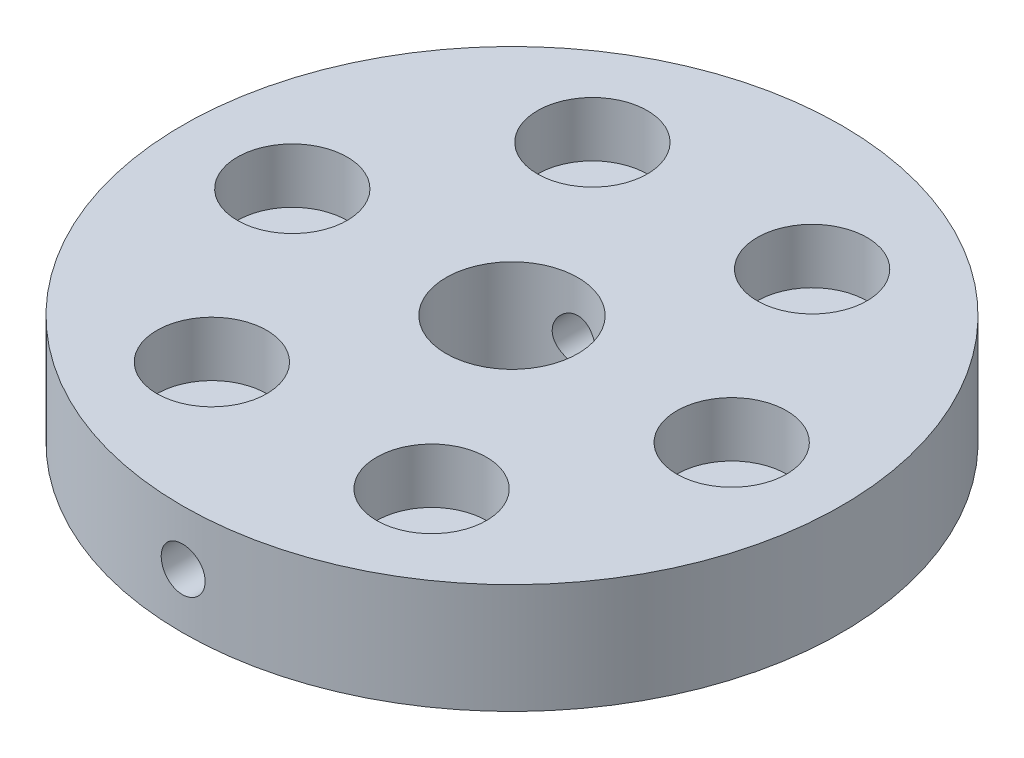
SolidWorks part; units mm, degrees
material "ABS"
ref_plane "Front Plane" through (0, 0, 0) normal (0, 0, 1) x (1, 0, 0)
ref_plane "Top Plane" through (0, 0, 0) normal (0, 1, 0) x (1, 0, 0)
ref_plane "Right Plane" through (0, 0, 0) normal (1, 0, 0) x (0, 0, -1)
sketch "Sketch1" plane through (0, 0, 0) normal (0, 1, 0) x (1, 0, 0)
  line L0 (0, 0) -> (108.2048, 0) construction
  circle A0 centre (0, 0) radius 30
  circle A1 centre (0, 0) radius 20 construction
  circle A2 centre (20, 0) radius 2
  circle A3 centre (10, -17.3205) radius 2
  circle A4 centre (-10, -17.3205) radius 2
  circle A5 centre (-20, 0) radius 2
  circle A6 centre (-10, 17.3205) radius 2
  circle A7 centre (10, 17.3205) radius 2
  circle A8 centre (0, 0) radius 6
  point P19 (0, 0)
  dimension "D1" = 60
  dimension "D2" = 40
  dimension "D3" = 4
  dimension "D5" = 12
  dimension "D4" = 6
extrude "Boss-Extrude1" add sketch "Sketch1" along normal blind 10
sketch "Sketch2" plane through (0, 0, 0) normal (0, 0, 1) x (1, 0, 0)
  line L0 (-30, 0) -> (30, 0) construction
  circle A0 centre (0, 5) radius 2
  dimension "D1" = 4
  dimension "D2" = 5
extrude "Cut-Extrude1" cut sketch "Sketch2" against normal through all and the other way through all
sketch "Sketch3" plane through (0, 10, 0) normal (0, 1, 0) x (1, 0, 0)
  circle A0 centre (0, 0) radius 20 construction
  circle A1 centre (-10, 17.3205) radius 5
  circle A2 centre (10, 17.3205) radius 5
  circle A3 centre (20, 0) radius 5
  circle A4 centre (10, -17.3205) radius 5
  circle A5 centre (-10, -17.3205) radius 5
  circle A6 centre (-20, 0) radius 5
  point P18 (0, 0)
  dimension "D1" = 40
  dimension "D2" = 10
  dimension "D3" = 6
extrude "Cut-Extrude2" cut sketch "Sketch3" against normal blind 5
